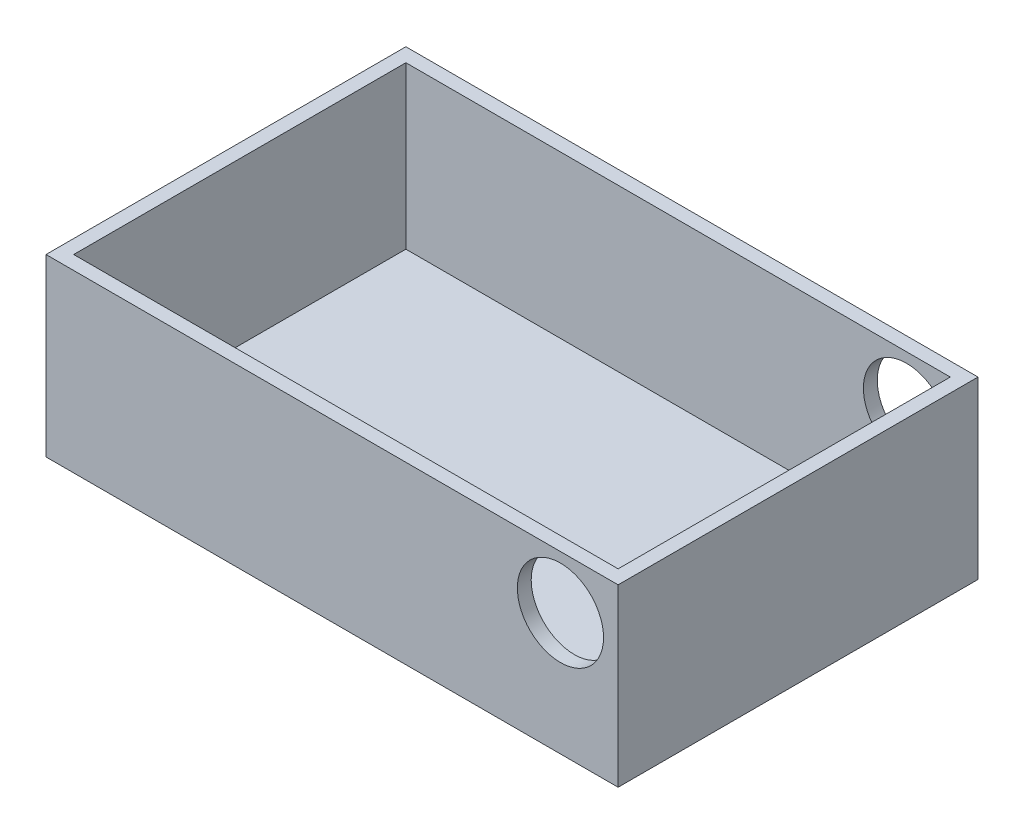
SolidWorks part; units mm, degrees
ref_plane "Front Plane" through (0, 0, 0) normal (0, 0, 1) x (1, 0, 0)
ref_plane "Top Plane" through (0, 0, 0) normal (0, 1, 0) x (1, 0, 0)
ref_plane "Right Plane" through (0, 0, 0) normal (1, 0, 0) x (0, 0, -1)
sketch "Sketch1" plane through (0, 0, 0) normal (0, 1, 0) x (1, 0, 0)
  line L1 (0, 0) -> (787.4, 0)
  line L2 (0, 0) -> (0, 495.3)
  line L3 (0, 495.3) -> (787.4, 495.3)
  line L4 (787.4, 0) -> (787.4, 495.3)
  dimension "D1" = 787.4
  dimension "D2" = 495.3
extrude "Boss-Extrude1" add sketch "Sketch1" along normal blind 241.3
shell "Shell1" thickness 19.05
sketch "Sketch2" plane through (0, 0, 0) normal (0, 0, 1) x (1, 0, 0)
  line L0 (0, 241.3) -> (0, 0) construction
  line L1 (0, 0) -> (787.4, 0) construction
  circle A0 centre (708.025, 168.275) radius 59.309
  dimension "D3" = 118.618
  dimension "D1" = 708.025
  dimension "D2" = 168.275
extrude "Cut-Extrude1" cut sketch "Sketch2" against normal through all
